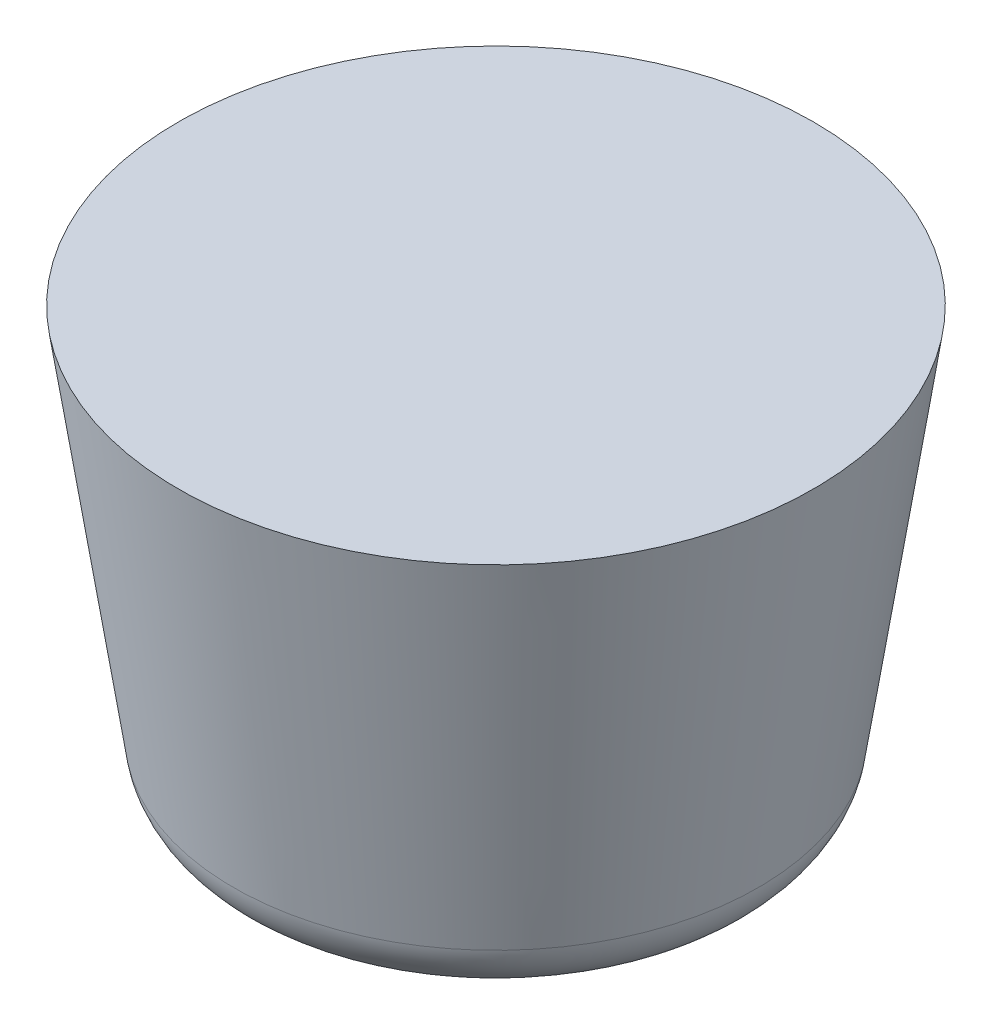
SolidWorks part; units mm, degrees
ref_plane "Alzado" through (0, 0, 0) normal (0, 0, 1) x (1, 0, 0)
ref_plane "Planta" through (0, 0, 0) normal (0, 1, 0) x (1, 0, 0)
ref_plane "Vista lateral" through (0, 0, 0) normal (1, 0, 0) x (0, 0, -1)
sketch "Croquis1" plane through (0, 0, 0) normal (0, 0, 1) x (1, 0, 0)
  line L0 (0, 0) -> (0, 20) construction
  line L1 (0, 20) -> (15, 20)
  line L2 (15, 20) -> (12, -0.2135)
  line L3 (12, -0.2135) -> (0, 0)
  line L4 (0, 0) -> (0, 20)
  dimension "D1" = 20
  dimension "D2" = 15
  dimension "D3" = 12
revolve "Revolución1" add sketch "Croquis1" angle 360 about L0
fillet "Redondeo1" radius 3 1 edges at (0, -0.2135, -12)
